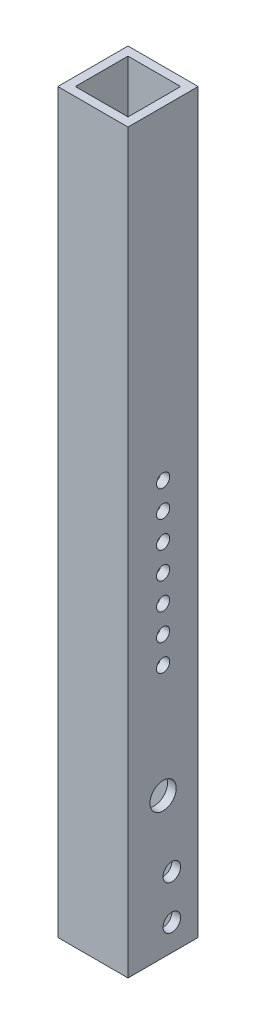
SolidWorks part; units mm, degrees
material "6061 Alloy"
ref_plane "Front Plane" through (0, 0, 0) normal (0, 0, 1) x (1, 0, 0)
ref_plane "Top Plane" through (0, 0, 0) normal (0, 1, 0) x (1, 0, 0)
ref_plane "Right Plane" through (0, 0, 0) normal (1, 0, 0) x (0, 0, -1)
sketch "Sketch1" plane through (0, 0, 0) normal (0, 1, 0) x (1, 0, 0)
  line L1 (-12.7, -12.7) -> (12.7, -12.7)
  line L2 (-12.7, -12.7) -> (-12.7, 12.7)
  line L3 (-12.7, 12.7) -> (12.7, 12.7)
  line L4 (12.7, -12.7) -> (12.7, 12.7)
  line L5 (-12.7, -12.7) -> (12.7, 12.7) construction
  line L6 (-12.7, 12.7) -> (12.7, -12.7) construction
  line L7 (-9.525, -9.525) -> (9.525, -9.525)
  line L8 (-9.525, -9.525) -> (-9.525, 9.525)
  line L9 (-9.525, 9.525) -> (9.525, 9.525)
  line L10 (9.525, -9.525) -> (9.525, 9.525)
  line L11 (-9.525, -9.525) -> (9.525, 9.525) construction
  line L12 (-9.525, 9.525) -> (9.525, -9.525) construction
  point P0 (0, 0)
  point P6 (0, 0)
  dimension "D1" = 25.4
  dimension "D2" = 25.4
  dimension "D3" = 19.05
extrude "Boss-Extrude1" add sketch "Sketch1" along normal blind 228.6 and the other way blind 38.1
sketch "Sketch3" plane through (0, 0, -12.7) normal (0, 0, -1) x (-1, 0, 0)
  line L1 (-5.08, 44.45) -> (5.08, 44.45)
  line L2 (-5.08, 44.45) -> (-5.08, 120.65)
  line L3 (-5.08, 120.65) -> (5.08, 120.65)
  line L4 (5.08, 44.45) -> (5.08, 120.65)
  line L5 (-5.08, 44.45) -> (5.08, 120.65) construction
  line L6 (-5.08, 120.65) -> (5.08, 44.45) construction
  point P0 (0, 82.55)
  dimension "D1" = 10.16
  dimension "D2" = 82.55
  dimension "D3" = 76.2
extrude "Cut-Extrude2" cut sketch "Sketch3" against normal up to next
sketch "Sketch4" plane through (12.7, 0, 0) normal (1, 0, 0) x (0, 0, -1)
  line L0 (-12.7, -38.1) -> (12.7, -38.1) construction
  line L1 (12.7, -38.1) -> (12.7, 228.6) construction
  circle A0 centre (0, 82.55) radius 2.3812
  circle A1 centre (0, 72.898) radius 2.3812
  circle A2 centre (0, 63.246) radius 2.3812
  circle A3 centre (0, 53.594) radius 2.3812
  circle A4 centre (0, 82.55) radius 2.3812
  circle A5 centre (0, 72.898) radius 2.3812
  circle A6 centre (0, 63.246) radius 2.3812
  circle A7 centre (0, 92.202) radius 2.3812
  circle A8 centre (0, 82.55) radius 2.3812
  circle A9 centre (0, 72.898) radius 2.3812
  circle A10 centre (0, 101.854) radius 2.3812
  circle A11 centre (0, 92.202) radius 2.3812
  circle A12 centre (0, 82.55) radius 2.3812
  circle A13 centre (0, 92.202) radius 2.3812
  circle A14 centre (0, 101.854) radius 2.3812
  circle A15 centre (0, 111.506) radius 2.3812
  circle A16 centre (3.175, -28.575) radius 3.175
  circle A17 centre (3.175, -12.7) radius 3.175
  circle A18 centre (0, 12.7) radius 4.7625
  point P39 (0, 0)
  point P40 (0, 0)
  dimension "D1" = 4.7625
  dimension "D7" = 6.35
  dimension "D10" = 9.525
  dimension "D2" = 82.55
  dimension "D5" = 15.875
  dimension "D6" = 9.525
  dimension "D8" = 9.652
  dimension "D9" = 9.652
  dimension "D11" = 12.7
  dimension "D12" = 9.525
  dimension "D3" = 4
  dimension "D4" = 4
extrude "Cut-Extrude3" cut sketch "Sketch4" against normal through all contours A16 | A17 | A2 | A1 | A0 | A10 | A15 | A18 | A3 | A7
